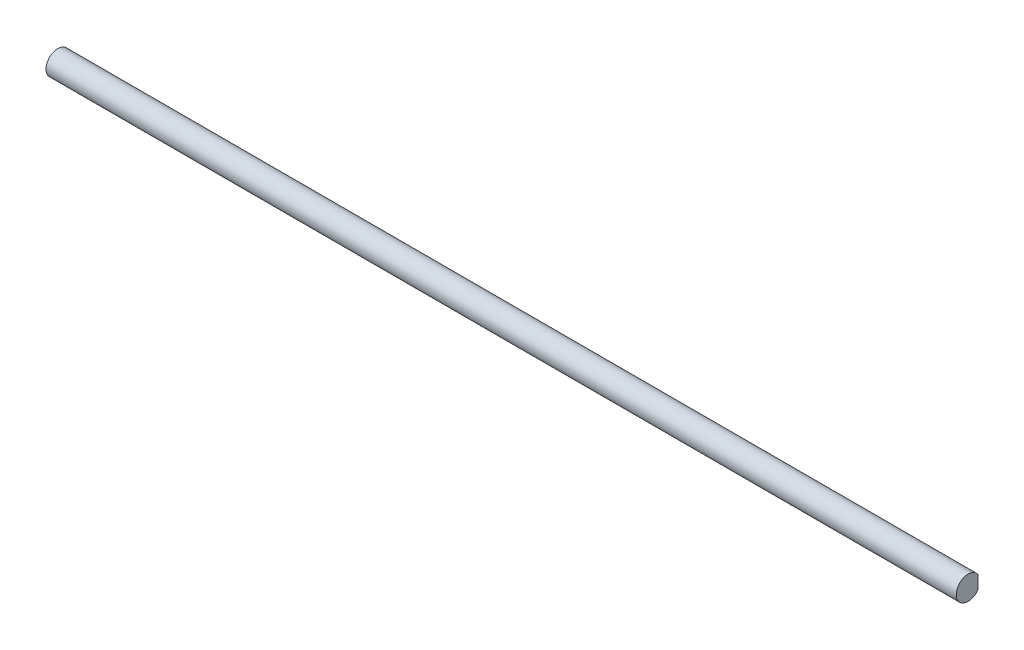
SolidWorks part; units mm, degrees
ref_plane "前视基准面" through (0, 0, 0) normal (0, 0, 1) x (1, 0, 0)
ref_plane "上视基准面" through (0, 0, 0) normal (0, 1, 0) x (1, 0, 0)
ref_plane "右视基准面" through (0, 0, 0) normal (1, 0, 0) x (0, 0, -1)
other "Configuration Table"
sketch "草图1" plane through (0, 0, 0) normal (1, 0, 0) x (0, 0, -1)
  circle A0 centre (0, 0) radius 6
extrude "凸台-拉伸1" add sketch "草图1" along normal blind 460
sketch "草图2" plane through (0, 0, 0) normal (0, 1, 0) x (1, 0, 0)
  line L0 (0, 6) -> (15.5, 6)
  line L1 (460, 6) -> (0, 6) construction
  line L2 (15.5, 6) -> (15.5, 5)
  line L3 (15.5, 5) -> (0, 5)
  line L4 (0, 6) -> (0, -6) construction
  line L5 (0, 5) -> (0, 6)
  dimension "D1" = 15.5
  dimension "D2" = 1
extrude "切除-拉伸1" cut sketch "草图2" against normal mid plane 400
ref_plane "基准面1" through (230, 0, 0) normal (-1, 0, 0) x (0, 0, 1)
mirror "镜向1" about plane through (230, 0, 0) normal (-1, 0, 0) of "切除-拉伸1"
sketch "草图4" plane through (0, 0, 0) normal (0, 1, 0) x (1, 0, 0)
  line L0 (104, 6) -> (104, 5)
  line L1 (444.5, 6) -> (15.5, 6) construction
  line L2 (104, 5) -> (120.5, 5)
  line L3 (120.5, 5) -> (120.5, 6)
  line L4 (120.5, 6) -> (104, 6)
  line L5 (0, 5) -> (0, -6) construction
  dimension "D1" = 16.5
  dimension "D2" = 1
  dimension "D3" = 104
extrude "切除-拉伸2" cut sketch "草图4" against normal mid plane 400
